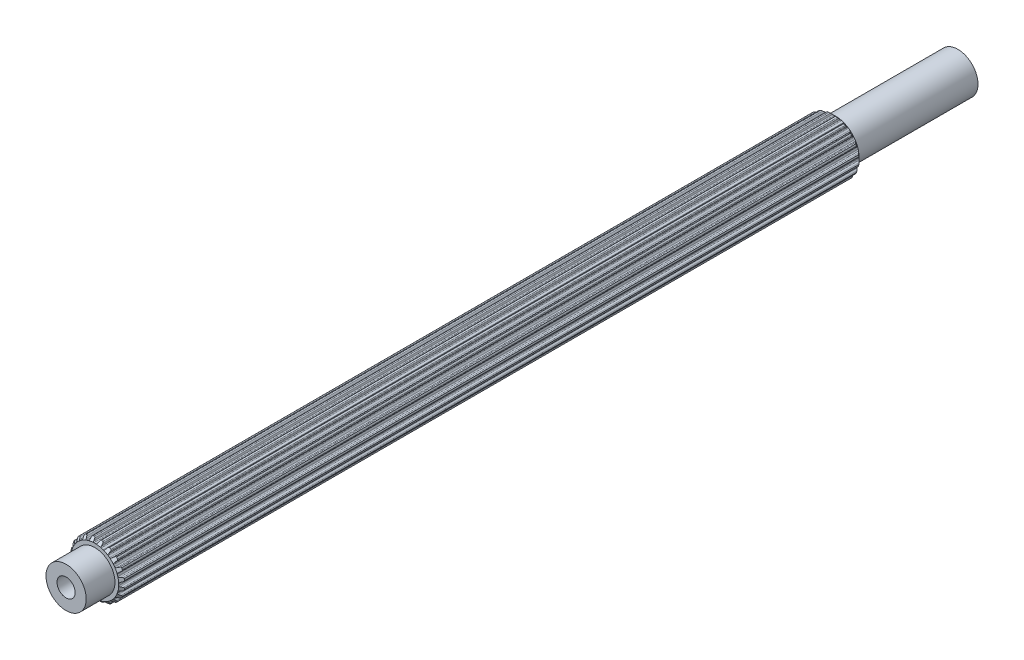
SolidWorks part; units mm, degrees
ref_plane "Front Plane" through (0, 0, 0) normal (0, 0, 1) x (1, 0, 0)
ref_plane "Top Plane" through (0, 0, 0) normal (0, 1, 0) x (1, 0, 0)
ref_plane "Right Plane" through (0, 0, 0) normal (1, 0, 0) x (0, 0, -1)
sketch "Sketch1" plane through (0, 0, 0) normal (0, 0, 1) x (1, 0, 0)
  line L0 (-0.1069, 2.9699) -> (0.1069, 2.9699)
  line L1 (0.3159, 3.2375) -> (0.2537, 3.0575)
  line L2 (-0.2964, 3.2367) -> (-0.2318, 3.0575)
  line L3 (-0.2964, 3.2367) -> (0.3159, 3.2375) construction
  line L4 (0, 3.3252) -> (0, 0) construction
  line L5 (-0.2318, 3.0575) -> (0.2537, 3.0575) construction
  line L6 (-0.4281, 3.3241) -> (0.4281, 3.3263) construction
  line L7 (0.7183, 3.1698) -> (0.7244, 2.9795)
  line L8 (0.816, 2.8576) -> (1.0195, 2.7915)
  line L9 (1.3009, 2.9815) -> (1.1862, 2.8295)
  line L10 (1.6627, 2.7927) -> (1.6097, 2.6099)
  line L11 (1.6591, 2.4655) -> (1.8322, 2.3398)
  line L12 (2.1585, 2.4335) -> (2.0025, 2.3245)
  line L13 (2.4443, 2.1423) -> (2.3374, 1.9847)
  line L14 (2.3398, 1.8322) -> (2.4655, 1.6591)
  line L15 (2.8049, 1.6474) -> (2.6228, 1.5919)
  line L16 (2.9866, 1.2821) -> (2.8363, 1.1653)
  line L17 (2.7915, 1.0195) -> (2.8576, 0.816)
  line L18 (3.1767, 0.7) -> (2.9863, 0.7035)
  line L19 (3.2367, 0.2964) -> (3.0575, 0.2318)
  line L20 (2.9699, 0.1069) -> (2.9699, -0.1069)
  line L21 (3.2375, -0.3159) -> (3.0575, -0.2537)
  line L22 (3.1698, -0.7183) -> (2.9795, -0.7244)
  line L23 (2.8576, -0.816) -> (2.7915, -1.0195)
  line L24 (2.9815, -1.3009) -> (2.8295, -1.1862)
  line L25 (2.7927, -1.6627) -> (2.6099, -1.6097)
  line L26 (2.4655, -1.6591) -> (2.3398, -1.8322)
  line L27 (2.4335, -2.1585) -> (2.3245, -2.0025)
  line L28 (2.1423, -2.4443) -> (1.9847, -2.3374)
  line L29 (1.8322, -2.3398) -> (1.6591, -2.4655)
  line L30 (1.6474, -2.8049) -> (1.5919, -2.6228)
  line L31 (1.2821, -2.9866) -> (1.1653, -2.8363)
  line L32 (1.0195, -2.7915) -> (0.816, -2.8576)
  line L33 (0.7, -3.1767) -> (0.7035, -2.9863)
  line L34 (0.2964, -3.2367) -> (0.2318, -3.0575)
  line L35 (0.1069, -2.9699) -> (-0.1069, -2.9699)
  line L36 (-0.3159, -3.2375) -> (-0.2537, -3.0575)
  line L37 (-0.7183, -3.1698) -> (-0.7244, -2.9795)
  line L38 (-0.816, -2.8576) -> (-1.0195, -2.7915)
  line L39 (-1.3009, -2.9815) -> (-1.1862, -2.8295)
  line L40 (-1.6627, -2.7927) -> (-1.6097, -2.6099)
  line L41 (-1.6591, -2.4655) -> (-1.8322, -2.3398)
  line L42 (-2.1585, -2.4335) -> (-2.0025, -2.3245)
  line L43 (-2.4443, -2.1423) -> (-2.3374, -1.9847)
  line L44 (-2.3398, -1.8322) -> (-2.4655, -1.6591)
  line L45 (-2.8049, -1.6474) -> (-2.6228, -1.5919)
  line L46 (-2.9866, -1.2821) -> (-2.8363, -1.1653)
  line L47 (-2.7915, -1.0195) -> (-2.8576, -0.816)
  line L48 (-3.1767, -0.7) -> (-2.9863, -0.7035)
  line L49 (-3.2367, -0.2964) -> (-3.0575, -0.2318)
  line L50 (-2.9699, -0.1069) -> (-2.9699, 0.1069)
  line L51 (-3.2375, 0.3159) -> (-3.0575, 0.2537)
  line L52 (-3.1698, 0.7183) -> (-2.9795, 0.7244)
  line L53 (-2.8576, 0.816) -> (-2.7915, 1.0195)
  line L54 (-2.9815, 1.3009) -> (-2.8295, 1.1862)
  line L55 (-2.7927, 1.6627) -> (-2.6099, 1.6097)
  line L56 (-2.4655, 1.6591) -> (-2.3398, 1.8322)
  line L57 (-2.4335, 2.1585) -> (-2.3245, 2.0025)
  line L58 (-2.1423, 2.4443) -> (-1.9847, 2.3374)
  line L59 (-1.8322, 2.3398) -> (-1.6591, 2.4655)
  line L60 (-1.6474, 2.8049) -> (-1.5919, 2.6228)
  line L61 (-1.2821, 2.9866) -> (-1.1653, 2.8363)
  line L62 (-1.0195, 2.7915) -> (-0.816, 2.8576)
  line L63 (-0.7, 3.1767) -> (-0.7035, 2.9863)
  line L64 (0.4281, 3.3263) -> (0.62, 3.2938)
  line L65 (1.4351, 3.0312) -> (1.6075, 2.9409)
  line L66 (2.3015, 2.4394) -> (2.4376, 2.3003)
  line L67 (2.9427, 1.6088) -> (3.0291, 1.4344)
  line L68 (3.2958, 0.6207) -> (3.3241, 0.4281)
  line L69 (3.3263, -0.4281) -> (3.2938, -0.62)
  line L70 (3.0312, -1.4351) -> (2.9409, -1.6075)
  line L71 (2.4394, -2.3015) -> (2.3003, -2.4376)
  line L72 (1.6088, -2.9427) -> (1.4344, -3.0291)
  line L73 (0.6207, -3.2958) -> (0.4281, -3.3241)
  line L74 (-0.4281, -3.3263) -> (-0.62, -3.2938)
  line L75 (-1.4351, -3.0312) -> (-1.6075, -2.9409)
  line L76 (-2.3015, -2.4394) -> (-2.4376, -2.3003)
  line L77 (-2.9427, -1.6088) -> (-3.0291, -1.4344)
  line L78 (-3.2958, -0.6207) -> (-3.3241, -0.4281)
  line L79 (-3.3263, 0.4281) -> (-3.2938, 0.62)
  line L80 (-3.0312, 1.4351) -> (-2.9409, 1.6075)
  line L81 (-2.4394, 2.3015) -> (-2.3003, 2.4376)
  line L82 (-1.6088, 2.9427) -> (-1.4344, 3.0291)
  line L83 (-0.6207, 3.2958) -> (-0.4281, 3.3241)
  arc A0 (0.2537, 3.0575) -> (0.1069, 2.9699) centre (0.1283, 3.1009) cw
  arc A1 (-0.2318, 3.0575) -> (-0.1069, 2.9699) centre (-0.1069, 3.1026) ccw
  arc A2 (0.62, 3.2938) -> (0.7183, 3.1698) centre (0.5856, 3.1656) cw
  arc A3 (0.7244, 2.9795) -> (0.816, 2.8576) centre (0.857, 2.9838) ccw
  arc A4 (-0.4281, 3.3241) -> (-0.2964, 3.2367) centre (-0.4213, 3.1916) cw
  arc A5 (0.4281, 3.3263) -> (0.3159, 3.2375) centre (0.4413, 3.1942) ccw
  arc A6 (1.1862, 2.8295) -> (1.0195, 2.7915) centre (1.0802, 2.9095) cw
  arc A7 (1.4351, 3.0312) -> (1.3009, 2.9815) centre (1.4068, 2.9015) ccw
  arc A8 (1.6075, 2.9409) -> (1.6627, 2.7927) centre (1.5352, 2.8297) cw
  arc A9 (1.6097, 2.6099) -> (1.6591, 2.4655) centre (1.7371, 2.5729) ccw
  arc A10 (2.0025, 2.3245) -> (1.8322, 2.3398) centre (1.9264, 2.4332) cw
  arc A11 (2.3015, 2.4394) -> (2.1585, 2.4335) centre (2.2346, 2.3248) ccw
  arc A12 (2.4376, 2.3003) -> (2.4443, 2.1423) centre (2.3345, 2.2168) cw
  arc A13 (2.3374, 1.9847) -> (2.3398, 1.8322) centre (2.4472, 1.9102) ccw
  arc A14 (2.6228, 1.5919) -> (2.4655, 1.6591) centre (2.5841, 1.7189) cw
  arc A15 (2.9427, 1.6088) -> (2.8049, 1.6474) centre (2.8436, 1.5205) ccw
  arc A16 (3.0291, 1.4344) -> (2.9866, 1.2821) centre (2.9052, 1.3869) cw
  arc A17 (2.8363, 1.1653) -> (2.7915, 1.0195) centre (2.9177, 1.0605) ccw
  arc A18 (2.9863, 0.7035) -> (2.8576, 0.816) centre (2.9887, 0.8362) cw
  arc A19 (3.2958, 0.6207) -> (3.1767, 0.7) centre (3.1743, 0.5673) ccw
  arc A20 (3.3241, 0.4281) -> (3.2367, 0.2964) centre (3.1916, 0.4213) cw
  arc A21 (3.0575, 0.2318) -> (2.9699, 0.1069) centre (3.1026, 0.1069) ccw
  arc A22 (3.0575, -0.2537) -> (2.9699, -0.1069) centre (3.1009, -0.1283) cw
  arc A23 (3.3263, -0.4281) -> (3.2375, -0.3159) centre (3.1942, -0.4413) ccw
  arc A24 (3.2938, -0.62) -> (3.1698, -0.7183) centre (3.1656, -0.5856) cw
  arc A25 (2.9795, -0.7244) -> (2.8576, -0.816) centre (2.9838, -0.857) ccw
  arc A26 (2.8295, -1.1862) -> (2.7915, -1.0195) centre (2.9095, -1.0802) cw
  arc A27 (3.0312, -1.4351) -> (2.9815, -1.3009) centre (2.9015, -1.4068) ccw
  arc A28 (2.9409, -1.6075) -> (2.7927, -1.6627) centre (2.8297, -1.5352) cw
  arc A29 (2.6099, -1.6097) -> (2.4655, -1.6591) centre (2.5729, -1.7371) ccw
  arc A30 (2.3245, -2.0025) -> (2.3398, -1.8322) centre (2.4332, -1.9264) cw
  arc A31 (2.4394, -2.3015) -> (2.4335, -2.1585) centre (2.3248, -2.2346) ccw
  arc A32 (2.3003, -2.4376) -> (2.1423, -2.4443) centre (2.2168, -2.3345) cw
  arc A33 (1.9847, -2.3374) -> (1.8322, -2.3398) centre (1.9102, -2.4472) ccw
  arc A34 (1.5919, -2.6228) -> (1.6591, -2.4655) centre (1.7189, -2.5841) cw
  arc A35 (1.6088, -2.9427) -> (1.6474, -2.8049) centre (1.5205, -2.8436) ccw
  arc A36 (1.4344, -3.0291) -> (1.2821, -2.9866) centre (1.3869, -2.9052) cw
  arc A37 (1.1653, -2.8363) -> (1.0195, -2.7915) centre (1.0605, -2.9177) ccw
  arc A38 (0.7035, -2.9863) -> (0.816, -2.8576) centre (0.8362, -2.9887) cw
  arc A39 (0.6207, -3.2958) -> (0.7, -3.1767) centre (0.5673, -3.1743) ccw
  arc A40 (0.4281, -3.3241) -> (0.2964, -3.2367) centre (0.4213, -3.1916) cw
  arc A41 (0.2318, -3.0575) -> (0.1069, -2.9699) centre (0.1069, -3.1026) ccw
  arc A42 (-0.2537, -3.0575) -> (-0.1069, -2.9699) centre (-0.1283, -3.1009) cw
  arc A43 (-0.4281, -3.3263) -> (-0.3159, -3.2375) centre (-0.4413, -3.1942) ccw
  arc A44 (-0.62, -3.2938) -> (-0.7183, -3.1698) centre (-0.5856, -3.1656) cw
  arc A45 (-0.7244, -2.9795) -> (-0.816, -2.8576) centre (-0.857, -2.9838) ccw
  arc A46 (-1.1862, -2.8295) -> (-1.0195, -2.7915) centre (-1.0802, -2.9095) cw
  arc A47 (-1.4351, -3.0312) -> (-1.3009, -2.9815) centre (-1.4068, -2.9015) ccw
  arc A48 (-1.6075, -2.9409) -> (-1.6627, -2.7927) centre (-1.5352, -2.8297) cw
  arc A49 (-1.6097, -2.6099) -> (-1.6591, -2.4655) centre (-1.7371, -2.5729) ccw
  arc A50 (-2.0025, -2.3245) -> (-1.8322, -2.3398) centre (-1.9264, -2.4332) cw
  arc A51 (-2.3015, -2.4394) -> (-2.1585, -2.4335) centre (-2.2346, -2.3248) ccw
  arc A52 (-2.4376, -2.3003) -> (-2.4443, -2.1423) centre (-2.3345, -2.2168) cw
  arc A53 (-2.3374, -1.9847) -> (-2.3398, -1.8322) centre (-2.4472, -1.9102) ccw
  arc A54 (-2.6228, -1.5919) -> (-2.4655, -1.6591) centre (-2.5841, -1.7189) cw
  arc A55 (-2.9427, -1.6088) -> (-2.8049, -1.6474) centre (-2.8436, -1.5205) ccw
  arc A56 (-3.0291, -1.4344) -> (-2.9866, -1.2821) centre (-2.9052, -1.3869) cw
  arc A57 (-2.8363, -1.1653) -> (-2.7915, -1.0195) centre (-2.9177, -1.0605) ccw
  arc A58 (-2.9863, -0.7035) -> (-2.8576, -0.816) centre (-2.9887, -0.8362) cw
  arc A59 (-3.2958, -0.6207) -> (-3.1767, -0.7) centre (-3.1743, -0.5673) ccw
  arc A60 (-3.3241, -0.4281) -> (-3.2367, -0.2964) centre (-3.1916, -0.4213) cw
  arc A61 (-3.0575, -0.2318) -> (-2.9699, -0.1069) centre (-3.1026, -0.1069) ccw
  arc A62 (-3.0575, 0.2537) -> (-2.9699, 0.1069) centre (-3.1009, 0.1283) cw
  arc A63 (-3.3263, 0.4281) -> (-3.2375, 0.3159) centre (-3.1942, 0.4413) ccw
  arc A64 (-3.2938, 0.62) -> (-3.1698, 0.7183) centre (-3.1656, 0.5856) cw
  arc A65 (-2.9795, 0.7244) -> (-2.8576, 0.816) centre (-2.9838, 0.857) ccw
  arc A66 (-2.8295, 1.1862) -> (-2.7915, 1.0195) centre (-2.9095, 1.0802) cw
  arc A67 (-3.0312, 1.4351) -> (-2.9815, 1.3009) centre (-2.9015, 1.4068) ccw
  arc A68 (-2.9409, 1.6075) -> (-2.7927, 1.6627) centre (-2.8297, 1.5352) cw
  arc A69 (-2.6099, 1.6097) -> (-2.4655, 1.6591) centre (-2.5729, 1.7371) ccw
  arc A70 (-2.3245, 2.0025) -> (-2.3398, 1.8322) centre (-2.4332, 1.9264) cw
  arc A71 (-2.4394, 2.3015) -> (-2.4335, 2.1585) centre (-2.3248, 2.2346) ccw
  arc A72 (-2.3003, 2.4376) -> (-2.1423, 2.4443) centre (-2.2168, 2.3345) cw
  arc A73 (-1.9847, 2.3374) -> (-1.8322, 2.3398) centre (-1.9102, 2.4472) ccw
  arc A74 (-1.5919, 2.6228) -> (-1.6591, 2.4655) centre (-1.7189, 2.5841) cw
  arc A75 (-1.6088, 2.9427) -> (-1.6474, 2.8049) centre (-1.5205, 2.8436) ccw
  arc A76 (-1.4344, 3.0291) -> (-1.2821, 2.9866) centre (-1.3869, 2.9052) cw
  arc A77 (-1.1653, 2.8363) -> (-1.0195, 2.7915) centre (-1.0605, 2.9177) ccw
  arc A78 (-0.7035, 2.9863) -> (-0.816, 2.8576) centre (-0.8362, 2.9887) cw
  arc A79 (-0.6207, 3.2958) -> (-0.7, 3.1767) centre (-0.5673, 3.1743) ccw
  point P14 (0, 2.9699)
  point P247 (0, 0)
  dimension "D4" = 0.1327
  dimension "D8" = 20
  dimension "D1" = 2.9699
  dimension "D2" = 0.2139
  dimension "D3" = 0.1904
  dimension "D5" = 0.0877
  dimension "D6" = 0.4855
  dimension "D7" = 0.8563
extrude "Boss-Extrude1" add sketch "Sketch1" along normal mid plane 92.0953
sketch "Sketch2" plane through (0, 0, 0) normal (0, 0, 1) x (1, 0, 0)
  circle A0 centre (0, 0) radius 2.5019
  dimension "D1" = 5.0038
extrude "Boss-Extrude2" add sketch "Sketch2" along normal blind 49.6291 and the other way blind 61.3131
sketch "Sketch4" plane through (0, 0, 49.6291) normal (0, 0, 1) x (1, 0, 0)
  circle A0 centre (0, 0) radius 2.5019 construction
  point P0 (0, 0)
sketch "Sketch5" plane through (0, 0, -61.3131) normal (0, 0, -1) x (-1, 0, 0)
  circle A0 centre (0, 0) radius 2.5019 construction
  point P0 (0, 0)
sketch "Sketch3" plane through (0, 0, 0) normal (1, 0, 0) x (0, 0, -1)
  line L0 (-44.9164, 4.1011) -> (-46.0477, 2.9699)
  line L1 (-46.0477, 2.9699) -> (-46.0477, 4.1011)
  line L2 (-46.0477, 4.1011) -> (-44.9164, 4.1011)
  line L3 (-46.0477, 2.5019) -> (-46.0477, -2.5019) construction
  line L5 (-14.3608, 0) -> (13.2171, 0) construction
  line L7 (46.0477, 42.7615) -> (46.0477, 2.9699)
  line L8 (46.0477, 2.9699) -> (26.1518, 22.8657)
  line L9 (26.1518, 22.8657) -> (46.0477, 42.7615)
  line L10 (46.0477, -2.5019) -> (46.0477, 2.5019) construction
  point P6 (-4.866, 6.1438)
  dimension "D1" = 45
  dimension "D2" = 45
revolve "Cut-Revolve1" cut sketch "Sketch3" angle 360 about L5
sketch "Sketch7" plane through (0, 0, 0) normal (0, 0, 1) x (1, 0, 0)
  circle A0 centre (0, 0) radius 1.1303
  point P2 (-0.0617, -8.5966)
  dimension "D1" = 2.2606
extrude "Cut-Extrude1" cut sketch "Sketch7" along normal up to surface and the other way up to surface up to face at (2.5019, 0, 49.6291) other way up to face at (2.5019, 0, -61.3131)
sketch "Sketch8" plane through (0, 0, 0) normal (0, 0, 1) x (1, 0, 0)
  circle A0 centre (0, 0) radius 1.1303
  circle A1 centre (0, 0) radius 1.1303 construction
  point P2 (-2.9839, -9.6344)
extrude "Boss-Extrude3" add sketch "Sketch8" along normal offset from surface 9.525 and the other way offset from surface (51.7881 mm away) 9.525 up to face at (1.1303, 0, 49.6291) other way up to face at (1.1303, 0, -61.3131)
